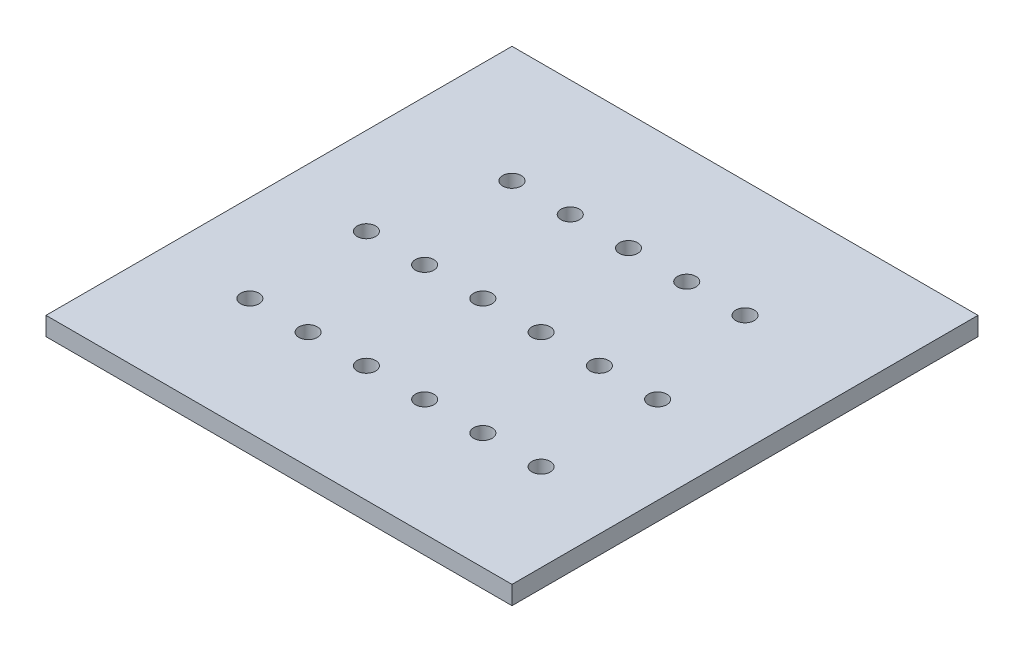
SolidWorks part; units mm, degrees
material "Oak"
ref_plane "Front Plane" through (0, 0, 0) normal (0, 0, 1) x (1, 0, 0)
ref_plane "Top Plane" through (0, 0, 0) normal (0, 1, 0) x (1, 0, 0)
ref_plane "Right Plane" through (0, 0, 0) normal (1, 0, 0) x (0, 0, -1)
sketch "Sketch1" plane through (0, 0, 0) normal (0, 1, 0) x (1, 0, 0)
  line L0 (0, 90) -> (120, 90) construction
  line L1 (0, 0) -> (120, 0)
  line L2 (0, 0) -> (0, 120)
  line L3 (0, 120) -> (120, 120)
  line L4 (120, 0) -> (120, 120)
  line L5 (0, 30) -> (120, 30) construction
  line L6 (0, 60) -> (120, 60) construction
  line L7 (30, 90) -> (45, 90) construction
  line L8 (60, 60) -> (60, 30) construction
  line L9 (0, 45) -> (120, 45) construction
  line L11 (22.5, 30) -> (37.5, 30) construction
  circle A0 centre (30, 90) radius 2.375
  circle A1 centre (45, 90) radius 2.375
  circle A2 centre (60, 90) radius 2.375
  circle A3 centre (75, 90) radius 2.375
  circle A4 centre (90, 90) radius 2.375
  circle A5 centre (97.5, 60) radius 2.375
  circle A6 centre (82.5, 60) radius 2.375
  circle A7 centre (67.5, 60) radius 2.375
  circle A8 centre (52.5, 60) radius 2.375
  circle A9 centre (37.5, 60) radius 2.375
  circle A10 centre (22.5, 30) radius 2.375
  circle A11 centre (37.5, 30) radius 2.375
  circle A12 centre (52.5, 30) radius 2.375
  circle A13 centre (67.5, 30) radius 2.375
  circle A14 centre (82.5, 30) radius 2.375
  circle A15 centre (97.5, 30) radius 2.375
  circle A16 centre (22.5, 60) radius 2.375
  point P26 (60, 45)
  dimension "D6" = 4.75
  dimension "D10" = 4.75
  dimension "D13" = 6
  dimension "D1" = 120
  dimension "D2" = 120
  dimension "D3" = 30
  dimension "D4" = 30
  dimension "D5" = 30
  dimension "D7" = 15
  dimension "D8" = 5
  dimension "D9" = 30
  dimension "D11" = 15
  dimension "D12" = 22.5
extrude "Boss-Extrude1" add sketch "Sketch1" along normal blind 4.7625
equation "\"LED_Diameter\"= 4.75"
